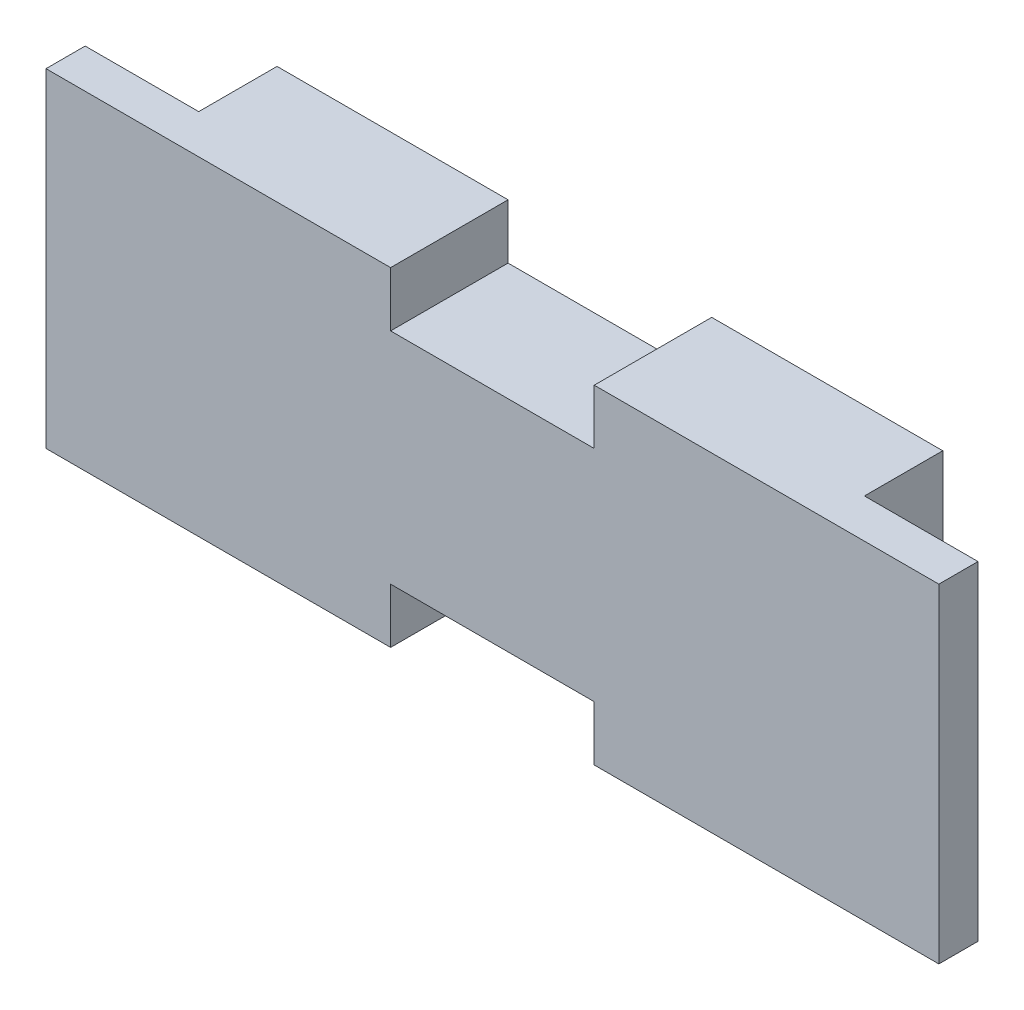
SolidWorks part; units mm, degrees
material "ABS"
ref_plane "Plan de face" through (0, 0, 0) normal (0, 0, 1) x (1, 0, 0)
ref_plane "Plan de dessus" through (0, 0, 0) normal (0, 1, 0) x (1, 0, 0)
ref_plane "Plan de droite" through (0, 0, 0) normal (1, 0, 0) x (0, 0, -1)
sketch "Sketch1" plane through (0, 0, 0) normal (0, 0, 1) x (1, 0, 0)
  line L1 (-28.5, -10.5) -> (28.5, -10.5)
  line L2 (-28.5, -10.5) -> (-28.5, 10.5)
  line L3 (-28.5, 10.5) -> (28.5, 10.5)
  line L4 (28.5, -10.5) -> (28.5, 10.5)
  line L5 (-28.5, -10.5) -> (28.5, 10.5) construction
  line L6 (-28.5, 10.5) -> (28.5, -10.5) construction
  point P0 (0, 0)
  dimension "D1" = 57
  dimension "D2" = 21
extrude "Boss-Extrude1" add sketch "Sketch1" along normal blind 2.5
sketch "Sketch2" plane through (0, 0, 0) normal (0, 0, -1) x (-1, 0, 0)
  line L0 (-28.5, 10.5) -> (28.5, 10.5) construction
  line L1 (-21.25, -10.5) -> (21.25, -10.5)
  line L2 (-21.25, -10.5) -> (-21.25, 10.5)
  line L3 (-21.25, 10.5) -> (21.25, 10.5)
  line L4 (21.25, -10.5) -> (21.25, 10.5)
  line L5 (-21.25, -10.5) -> (21.25, 10.5) construction
  line L6 (-21.25, 10.5) -> (21.25, -10.5) construction
  point P0 (0, 0)
  dimension "D1" = 42.5
extrude "Boss-Extrude2" add sketch "Sketch2" along normal blind 5
sketch "Sketch3" plane through (0, 0, 2.5) normal (0, 0, 1) x (1, 0, 0)
  line L0 (28.5, 10.5) -> (-28.5, 10.5) construction
  line L1 (-6.5, 7) -> (6.5, 7)
  line L2 (-6.5, 7) -> (-6.5, 10.5)
  line L3 (-6.5, 10.5) -> (6.5, 10.5)
  line L4 (6.5, 7) -> (6.5, 10.5)
  line L5 (-6.5, 7) -> (6.5, 10.5) construction
  line L6 (-6.5, 10.5) -> (6.5, 7) construction
  point P0 (0, 8.75)
  point P7 (0, 0)
  dimension "D1" = 13
  dimension "D2" = 3.5
extrude "Cut-Extrude1" cut sketch "Sketch3" against normal through all
mirror "Mirror1" about plane through (0, 0, 0) normal (0, 1, 0) of "Cut-Extrude1"
